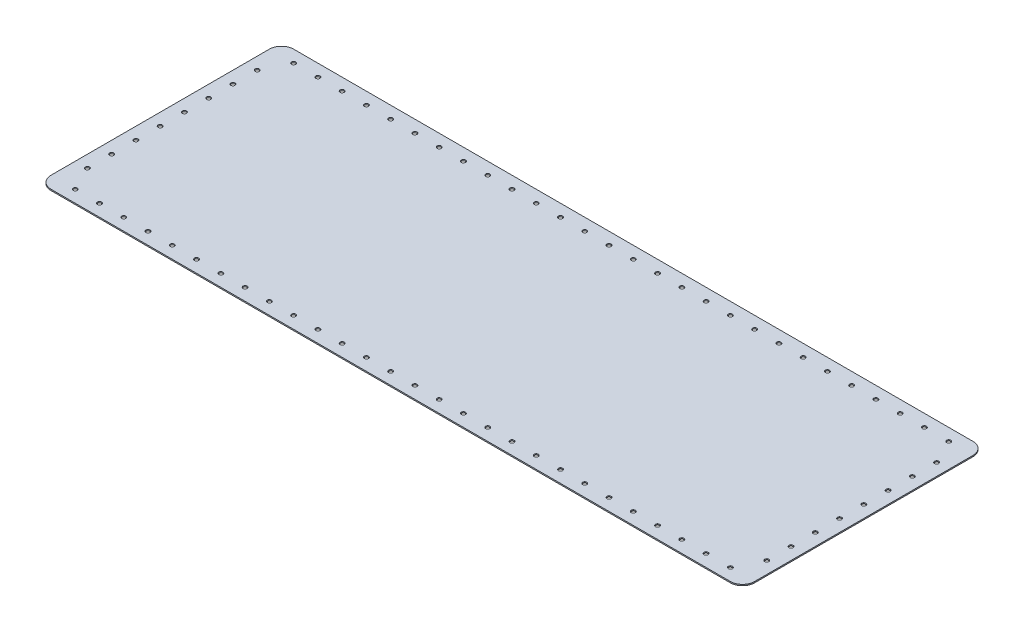
SolidWorks part; units mm, degrees
material "3003-H12"
ref_plane "Front Plane" through (0, 0, 0) normal (0, 0, 1) x (1, 0, 0)
ref_plane "Top Plane" through (0, 0, 0) normal (0, 1, 0) x (1, 0, 0)
ref_plane "Right Plane" through (0, 0, 0) normal (1, 0, 0) x (0, 0, -1)
sketch "Sketch1" plane through (0, 0, 0) normal (0, 1, 0) x (1, 0, 0)
  line L1 (-290, 100) -> (290, 100)
  line L2 (-290, 100) -> (-290, -100)
  line L3 (-290, -100) -> (290, -100)
  line L4 (290, 100) -> (290, -100)
  line L5 (-290, 100) -> (290, -100) construction
  line L6 (-290, -100) -> (290, 100) construction
  point P0 (0, 0)
  dimension "D1" = 580
  dimension "D2" = 200
extrude "Boss-Extrude1" add sketch "Sketch1" along normal blind 1
fillet "Fillet1" radius 10 4 edges at (-290, 0.5, 100) (290, 0.5, 100) (290, 0.5, -100) (-290, 0.5, -100)
hole_wizard "M3 Clearance Hole1" positions "Sketch2" profile "Sketch3" hole size "M3" standard "ANSI Metric" end condition through all
sketch "Sketch2" plane through (0, 1, 0) normal (0, 1, 0) x (1, 0, 0)
  line L0 (280, 100) -> (-280, 100) construction
  line L1 (290, -90) -> (290, 90) construction
  line L2 (-0.55, 0) -> (0.55, 0) construction
  line L3 (0, -0.55) -> (0, 0.55) construction
  point P1 (280, 70)
  point P3 (270, 90)
  point P17 (250, 90)
  point P18 (230, 90)
  point P19 (210, 90)
  point P20 (190, 90)
  point P21 (170, 90)
  point P22 (150, 90)
  point P23 (130, 90)
  point P24 (110, 90)
  point P25 (90, 90)
  point P26 (70, 90)
  point P27 (50, 90)
  point P28 (30, 90)
  point P29 (10, 90)
  point P30 (-10, 90)
  point P31 (-30, 90)
  point P32 (-50, 90)
  point P33 (-70, 90)
  point P34 (-90, 90)
  point P35 (-110, 90)
  point P36 (-130, 90)
  point P37 (-150, 90)
  point P38 (-170, 90)
  point P39 (-190, 90)
  point P40 (-210, 90)
  point P41 (-230, 90)
  point P42 (-250, 90)
  point P43 (-270, 90)
  point P51 (280, 50.003)
  point P52 (280, 30.0061)
  point P53 (280, 10.0091)
  point P54 (280, -9.9878)
  point P55 (280, -29.9848)
  point P56 (280, -49.9817)
  point P57 (280, -69.9787)
  point P60 (270, -90)
  point P61 (250, -90)
  point P62 (230, -90)
  point P63 (210, -90)
  point P64 (190, -90)
  point P65 (170, -90)
  point P66 (150, -90)
  point P67 (130, -90)
  point P68 (110, -90)
  point P69 (90, -90)
  point P70 (70, -90)
  point P71 (50, -90)
  point P72 (30, -90)
  point P73 (10, -90)
  point P74 (-10, -90)
  point P75 (-30, -90)
  point P76 (-50, -90)
  point P77 (-70, -90)
  point P78 (-90, -90)
  point P79 (-110, -90)
  point P80 (-130, -90)
  point P81 (-150, -90)
  point P82 (-170, -90)
  point P83 (-190, -90)
  point P84 (-210, -90)
  point P85 (-230, -90)
  point P86 (-250, -90)
  point P87 (-270, -90)
  point P90 (-280, 70)
  point P91 (-280, 50.003)
  point P92 (-280, 30.0061)
  point P93 (-280, 10.0091)
  point P94 (-280, -9.9878)
  point P95 (-280, -29.9848)
  point P96 (-280, -49.9817)
  point P97 (-280, -69.9787)
  dimension "D1" = 30
  dimension "D2" = 10
  dimension "D3" = 20
  dimension "D4" = 10
  dimension "D6" = 20
  dimension "D8" = 19.997
  dimension "D5" = 28
  dimension "D7" = 8
sketch "Sketch3" plane through (280, 1, -70) normal (1, 0, 0) x (0, 0, 1)
  line L0 (0, 0) -> (0, 1)
  line L1 (0, 1) -> (1.7, 1)
  line L2 (1.7, 1) -> (1.7, 0.025)
  line L3 (1.7, 0.025) -> (1.725, 0)
  line L5 (1.725, 0) -> (0, 0)
  line L6 (-1.7, 0.025) -> (-1.725, 0) construction
  line L11 (0, -6.35) -> (0, 107.95) construction
  dimension "Thru Hole Dia." = 3.4
  dimension "Thru Hole Depth" = 1
  dimension "Near C'Sink Dia." = 3.45
  dimension "Near C'Sink Angle" = 90
